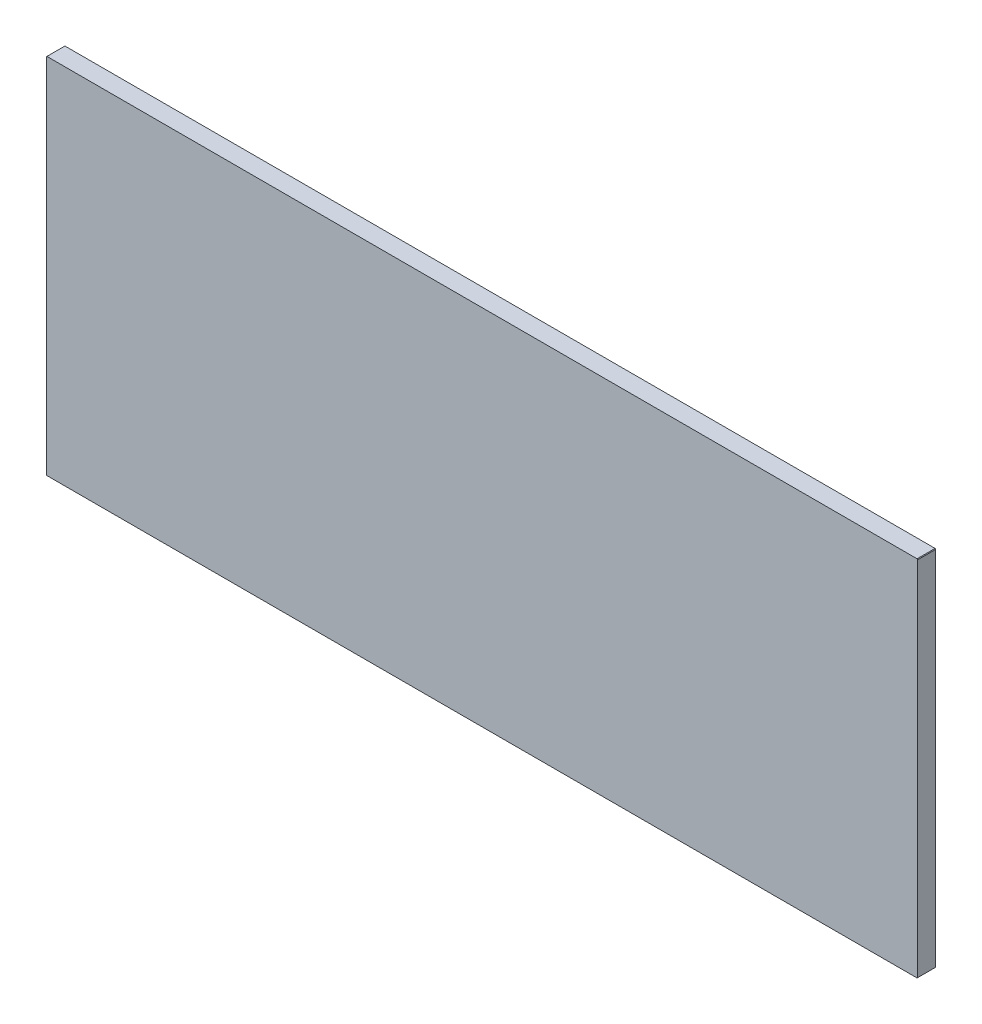
SolidWorks part; units mm, degrees
material "302 SSTL"
ref_plane "Front" through (0, 0, 0) normal (0, 0, 1) x (1, 0, 0)
ref_plane "Top" through (0, 0, 0) normal (0, 1, 0) x (1, 0, 0)
ref_plane "Right" through (0, 0, 0) normal (1, 0, 0) x (0, 0, -1)
sketch "Sketch1" plane through (0, 0, 0) normal (0, 0, 1) x (1, 0, 0)
  line L0 (-38.0746, 15.875) -> (-38.1, 15.8496)
  line L1 (-0.0254, 0) -> (-38.0746, 0)
  line L2 (0, 0.0254) -> (0, 15.8496)
  line L3 (-0.0254, 15.875) -> (-38.0746, 15.875)
  line L4 (-38.1, 0.0254) -> (-38.1, 15.8496)
  line L5 (-38.0746, 0) -> (-38.1, 0.0254)
  line L6 (0, 0.0254) -> (-0.0254, 0)
  line L7 (0, 15.8496) -> (-0.0254, 15.875)
  point P5 (-38.1, 15.875)
  point P9 (-38.1, 15.875)
  point P12 (-38.1, 0)
  point P15 (0, 15.875)
  point P18 (0, 0)
  point P19 (-38.1, 0)
  point P22 (0, 0)
  point P25 (0, 15.875)
  dimension "D5" = 0.0254
  dimension "D6" = 0.0254
  dimension "D1" = 15.875
  dimension "D2" = 38.1
  dimension "D7" = 0.0254
  dimension "D8" = 0.0254
extrude "Extrude1" add sketch "Sketch1" along normal blind 0.7874
